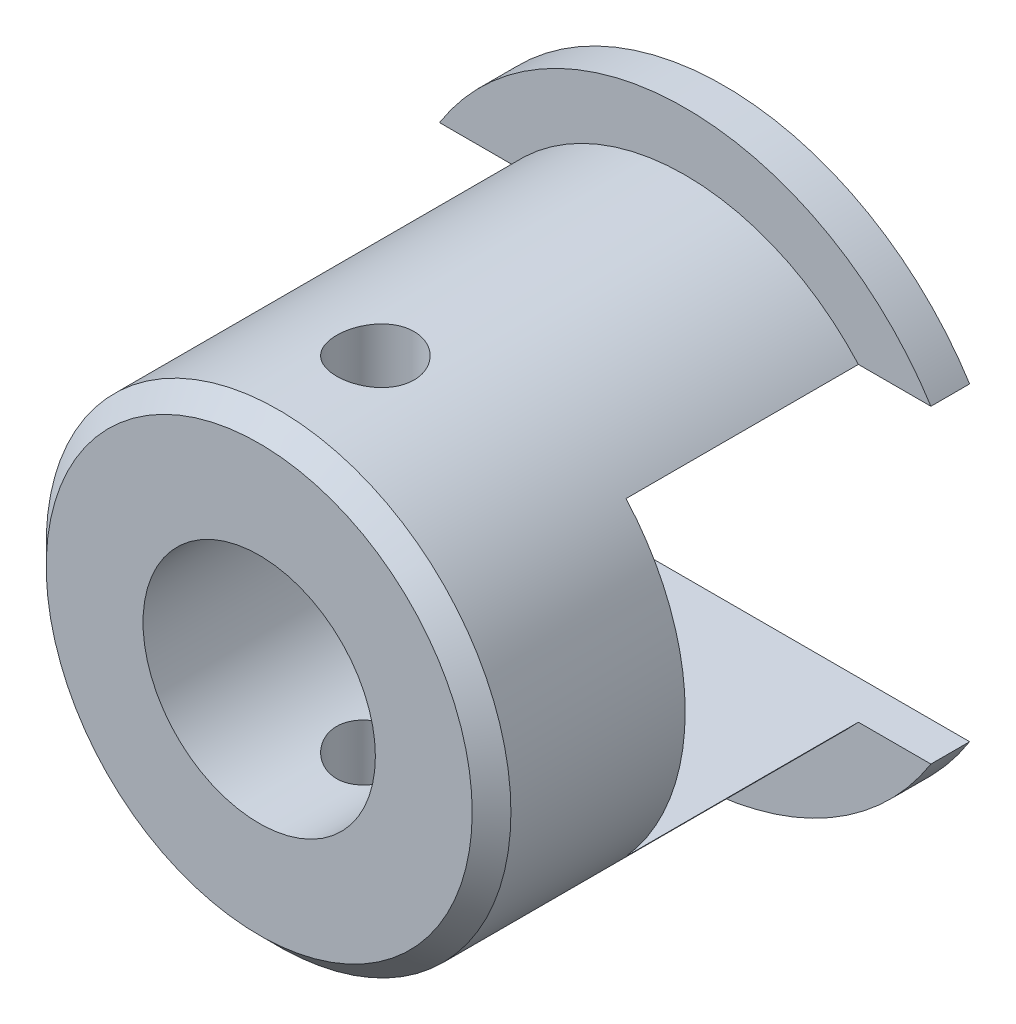
SolidWorks part; units mm, degrees
ref_plane "Plan de face" through (0, 0, 0) normal (0, 0, 1) x (1, 0, 0)
ref_plane "Plan de dessus" through (0, 0, 0) normal (0, 1, 0) x (1, 0, 0)
ref_plane "Plan de droite" through (0, 0, 0) normal (1, 0, 0) x (0, 0, -1)
sketch "Esquisse1" plane through (0, 0, 0) normal (0, 0, 1) x (1, 0, 0)
  circle A0 centre (0, 0) radius 7.5
  dimension "D1" = 15
extrude "Boss.-Extru.1" add sketch "Esquisse1" along normal blind 12
sketch "Esquisse2" plane through (0, 0, 12) normal (0, 0, 1) x (1, 0, 0)
  circle A0 centre (0, 0) radius 7.5
  circle A1 centre (0, 0) radius 6
  dimension "D1" = 15
  dimension "D2" = 12
extrude "Enlèv. mat.-Extru.1" cut sketch "Esquisse2" against normal blind 11
sketch "Esquisse3" plane through (0, 0, 12) normal (0, 0, 1) x (1, 0, 0)
  circle A0 centre (0, 0) radius 3
  dimension "D1" = 6
extrude "Enlèv. mat.-Extru.2" cut sketch "Esquisse3" against normal blind 5
sketch "Esquisse4" plane through (0, 0, 0) normal (0, 0, -1) x (-1, 0, 0)
  line L1 (-9.8848, -4) -> (9.8848, -4)
  line L2 (-9.8848, -4) -> (-9.8848, 4)
  line L3 (-9.8848, 4) -> (9.8848, 4)
  line L4 (9.8848, -4) -> (9.8848, 4)
  line L5 (-9.8848, -4) -> (9.8848, 4) construction
  line L6 (-9.8848, 4) -> (9.8848, -4) construction
  point P0 (0, 0)
  dimension "D1" = 8
extrude "Enlèv. mat.-Extru.3" cut sketch "Esquisse4" against normal blind 7
sketch "Esquisse5" plane through (0, 0, 0) normal (0, 1, 0) x (1, 0, 0)
  line L0 (0, 0) -> (0, -12) construction
  line L1 (6.3443, 0) -> (-6.3443, 0) construction
  line L2 (-6, -12) -> (6, -12) construction
  circle A0 centre (0, -9) radius 1
  dimension "D1" = 2
  dimension "D2" = 3
extrude "Enlèv. mat.-Extru.4" cut sketch "Esquisse5" against normal blind 7 and the other way blind 7
chamfer "Chanfrein1" distance 0.5 angle 45 1 edges at (6, 0, 12)
